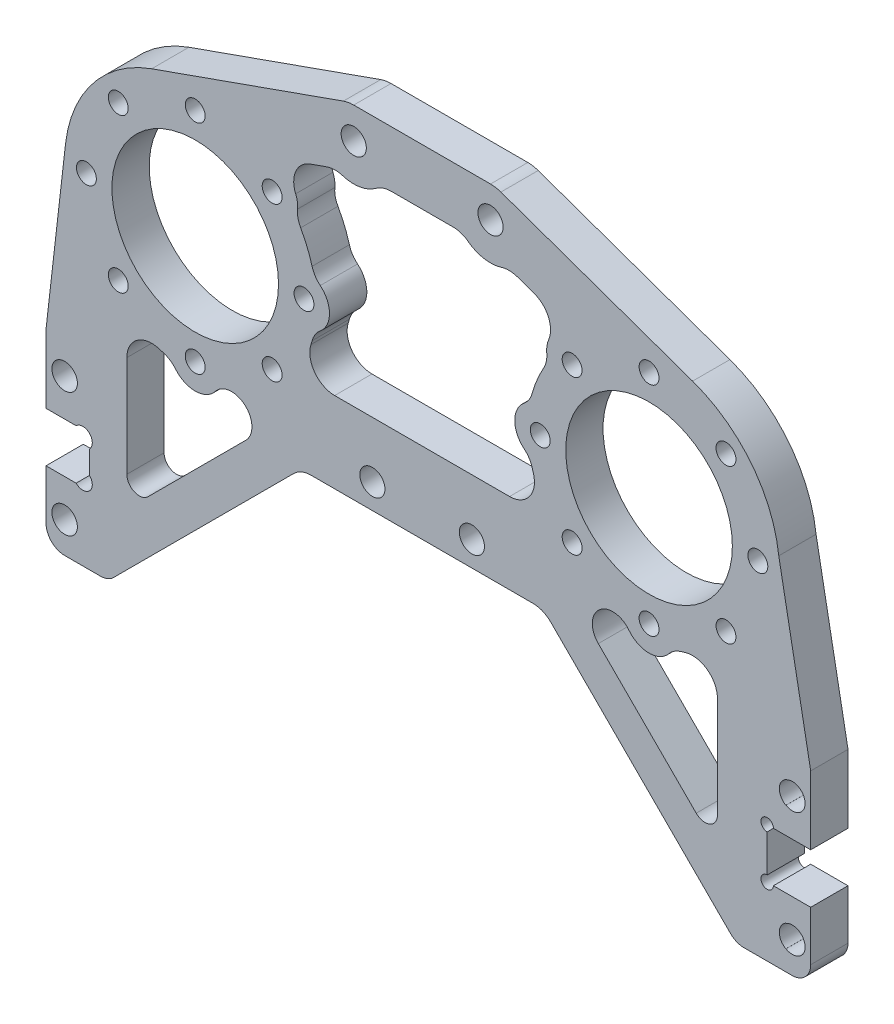
SolidWorks part; units mm, degrees
material "Thornel Mat VMA"
ref_plane "前视基准面" through (0, 0, 0) normal (0, 0, 1) x (1, 0, 0)
ref_plane "上视基准面" through (0, 0, 0) normal (0, 1, 0) x (1, 0, 0)
ref_plane "右视基准面" through (0, 0, 0) normal (1, 0, 0) x (0, 0, -1)
sketch "草图1" plane through (0, 0, 0) normal (0, 0, 1) x (1, 0, 0)
  line L0 (-36.5, 0) -> (36.5, 0) construction
  line L1 (-43.5079, -19.7962) -> (-12.6685, -30.7134)
  line L2 (11, -26) -> (-11, -26) construction
  line L3 (11, -26) -> (11, 26) construction
  line L4 (11, 26) -> (-11, 26) construction
  line L5 (-11, -26) -> (-11, 26) construction
  line L6 (11, -26) -> (-11, 26) construction
  line L7 (11, 26) -> (-11, -26) construction
  line L8 (-11, -31) -> (11, -31)
  line L9 (12.6685, -30.7134) -> (43.5079, -19.7962)
  line L10 (43.5079, 19.7962) -> (12.6685, 30.7134)
  line L11 (11, 31) -> (-11, 31)
  line L12 (-12.6685, 30.7134) -> (-43.5079, 19.7962)
  line L13 (0, 26) -> (0, -20) construction
  line L14 (0, -20) -> (-8, -20) construction
  circle A0 centre (-11, 26) radius 2.025
  circle A1 centre (11, 26) radius 2.025
  circle A2 centre (11, -26) radius 2.025 construction
  circle A3 centre (-11, -26) radius 2.025 construction
  circle A4 centre (-36.5, 0) radius 13.4
  circle A5 centre (-36.5, 0) radius 17.5 construction
  circle A6 centre (-19, 0) radius 1.6
  circle A7 centre (-24.1256, -12.3744) radius 1.6
  circle A8 centre (-36.5, -17.5) radius 1.6
  circle A9 centre (-48.8744, -12.3744) radius 1.6
  circle A10 centre (-54, 0) radius 1.6
  circle A11 centre (-48.8744, 12.3744) radius 1.6
  circle A12 centre (-36.5, 17.5) radius 1.6
  circle A13 centre (-24.1256, 12.3744) radius 1.6
  circle A14 centre (36.5, 0) radius 13.4
  circle A15 centre (36.5, 0) radius 17.5 construction
  circle A16 centre (19, 0) radius 1.6
  circle A17 centre (24.1256, 12.3744) radius 1.6
  circle A18 centre (36.5, 17.5) radius 1.6
  circle A19 centre (48.8744, 12.3744) radius 1.6
  circle A20 centre (54, 0) radius 1.6
  circle A21 centre (48.8744, -12.3744) radius 1.6
  circle A22 centre (36.5, -17.5) radius 1.6
  circle A23 centre (24.1256, -12.3744) radius 1.6
  arc A24 (43.5079, -19.7962) -> (43.5079, 19.7962) centre (36.5, 0) ccw
  arc A25 (-43.5079, -19.7962) -> (-43.5079, 19.7962) centre (-36.5, 0) cw
  arc A26 (12.6685, 30.7134) -> (11, 31) centre (11, 26) ccw
  arc A27 (-11, 31) -> (-12.6685, 30.7134) centre (-11, 26) ccw
  arc A28 (11, -31) -> (12.6685, -30.7134) centre (11, -26) ccw
  arc A29 (-12.6685, -30.7134) -> (-11, -31) centre (-11, -26) ccw
  circle A30 centre (-8, -20) radius 2.025
  circle A31 centre (8, -20) radius 2.025
  point P3 (0, 0)
  point P32 (-36.5, 0)
  point P51 (36.5, 0)
  dimension "D4" = 4.05
  dimension "D5" = 26.8
  dimension "D6" = 35
  dimension "D7" = 3.2
  dimension "D10" = 21
  dimension "D11" = 5
  dimension "D13" = 16
  dimension "D1" = 73
  dimension "D2" = 22
  dimension "D3" = 52
  dimension "D12" = 46
  dimension "D8" = 8
  dimension "D9" = 8
extrude "凸台-拉伸1" add sketch "草图1" along normal blind 6
chamfer "倒角1" distance 2.2 angle 45 2 edges at (-8.975, 26, 0) (13.025, 26, 0)
sketch "草圖2" plane through (0, 0, 0) normal (0, 0, -1) x (-1, 0, 0)
  line L9 (60.5, -55) -> (0, -55)
  line L10 (0, -55) -> (0, -31)
  line L11 (11, -31) -> (-11, -31) construction
  line L12 (0, -31) -> (43.5079, -19.7962)
  line L13 (43.5079, -19.7962) -> (12.6685, -30.7134) construction
  line L14 (57.5, -30) -> (57.5, -50) construction
  line L15 (60.5, -44) -> (53.5, -44)
  line L17 (60.5, -36) -> (53.5, -36)
  line L18 (53.5, -44) -> (53.5, -36)
  line L19 (60.5, -55) -> (60.5, -44)
  line L20 (60.5, -36) -> (60.5, -25)
  line L21 (0, 0) -> (0, 58.3141) construction
  line L22 (60.5, -25) -> (57.3637, 2.3891)
  arc A0 (39.9252, -20.7188) -> (57.5, 0) centre (36.5, 0) ccw construction
  arc A2 (43.5079, -19.7962) -> (43.5079, 19.7962) centre (36.5, 0) ccw construction
  circle A3 centre (36.5, 0) radius 21 construction
  arc A4 (43.5079, -19.7962) -> (57.3637, 2.3891) centre (36.5, 0) ccw
  circle A6 centre (57.5, -40) radius 4 construction
  circle A7 centre (57.5, -30) radius 2.05
  circle A8 centre (57.5, -50) radius 2.05
  dimension "D3" = 115
  dimension "D4" = 8
  dimension "D5" = 4.1
  dimension "D1" = 3
  dimension "D2" = 40
  dimension "D6" = 20
  dimension "D7" = 24
extrude "填料-伸長1" add sketch "草圖2" against normal up to surface (6 mm away)
sketch "草图3" plane through (0, 0, 0) normal (0, 0, -1) x (-1, 0, 0)
  line L4 (60.5, -55) -> (60.5, -44) construction
  line L6 (50.5, -55) -> (20.6716, -25.1716)
  line L11 (17.8431, -24) -> (0, -24)
  line L13 (0, -24) -> (0, -55)
  line L14 (0, -55) -> (50.5, -55)
  circle A0 centre (8, -20) radius 2.025 construction
  arc A1 (20.6716, -25.1716) -> (17.8431, -24) centre (17.8431, -28) ccw
  dimension "D4" = 4
  dimension "D3" = 4
  dimension "D1" = 45
  dimension "D2" = 10
extrude "切除-拉伸2" cut sketch "草图3" against normal through all
sketch "草图4" plane through (0, 0, 0) normal (0, 0, -1) x (-1, 0, 0)
  line L0 (55.6567, -36) -> (53.5, -38.1567) construction
  line L3 (53.5, -41.8433) -> (55.6567, -44) construction
  line L5 (60.5, -36) -> (53.5, -36) construction
  line L6 (53.5, -44) -> (53.5, -36) construction
  line L7 (60.5, -44) -> (53.5, -44) construction
  circle A0 centre (54.5783, -42.9217) radius 1.525
  circle A1 centre (54.5783, -37.0783) radius 1.525
  dimension "D1" = 3.05
  dimension "D2" = 45
  dimension "D3" = 45
extrude "切除-拉伸3" cut sketch "草图4" against normal through all
mirror "鏡射2" about plane through (0, 0, 0) normal (1, 0, 0) of "切除-拉伸3", "填料-伸長1", "切除-拉伸2"
fillet "圆角1" radius 3 4 edges at (60.5, -55, 3) (50.5, -55, 3) (-50.5, -55, 3) (-60.5, -55, 3)
sketch "草图5" plane through (0, 0, 0) normal (0, 0, -1) x (-1, 0, 0)
  line L0 (8, -20) -> (-8, -20) construction
  line L2 (-2, -25.5) -> (1, -25.5)
  line L3 (2, -24.5) -> (2, -6.5)
  line L4 (1, -5.5) -> (-2, -5.5)
  line L5 (-3, -24.5) -> (-3, -6.5)
  arc A0 (-2, -25.5) -> (-3, -24.5) centre (-2, -24.5) cw
  arc A1 (1, -5.5) -> (2, -6.5) centre (1, -6.5) cw
  arc A2 (1, -25.5) -> (2, -24.5) centre (1, -24.5) ccw
  arc A3 (-3, -6.5) -> (-2, -5.5) centre (-2, -6.5) cw
  point P11 (-0.5, -5.5)
  point P14 (-3, -25.5)
  point P17 (2, -5.5)
  point P20 (2, -25.5)
  point P23 (-3, -5.5)
  dimension "D4" = 1
  dimension "D1" = 5
  dimension "D2" = 5.5
  dimension "D3" = 20
  dimension "D5" = 2
extrude "切除-拉伸4" [suppressed] cut sketch "草图5" against normal through all
sketch "草图9" plane through (0, 0, 0) normal (0, 0, -1) x (-1, 0, 0)
  line L0 (47.5, -38.6863) -> (47.5, -22.4332)
  line L2 (28.3372, -24.3519) -> (44.0858, -40.1005)
  line L3 (0, 44.0083) -> (0, -69.3597) construction
  line L4 (-14.0668, -11) -> (14.0668, -11)
  line L5 (49.6213, -54.1213) -> (20.6716, -25.1716) construction
  line L9 (53.5, -41.8433) -> (53.5, -38.1567) construction
  line L10 (17.9923, 19.2815) -> (15.3212, 20.227)
  line L12 (-5, 22) -> (5, 22)
  line L14 (12.6685, 30.7134) -> (43.5079, 19.7962) construction
  line L15 (-11, 31) -> (11, 31) construction
  line L19 (17.8431, -24) -> (-17.8431, -24) construction
  line L20 (-17.9923, 19.2815) -> (-15.3212, 20.227)
  line L21 (-28.3372, -24.3519) -> (-44.0858, -40.1005)
  line L22 (-47.5, -38.6863) -> (-47.5, -22.4332)
  arc A1 (33.26, -20.0125) -> (28.3372, -24.3519) centre (30.662, -22.0272) ccw
  arc A2 (47.5, -38.6863) -> (44.0858, -40.1005) centre (45.5, -38.6863) cw
  arc A3 (7.4, 21.2) -> (12.7918, 20.2738) centre (11, 26) ccw
  arc A4 (19.5414, 9.6258) -> (17.702, 5.1851) centre (36.5, 0) ccw
  arc A6 (5, 22) -> (7.4, 21.2) centre (5, 18) cw
  arc A7 (15.3212, 20.227) -> (12.7918, 20.2738) centre (13.9864, 16.4563) ccw
  arc A8 (17.9923, 19.2815) -> (20.3455, 13.9619) centre (16.6575, 15.5108) cw
  arc A9 (14.0668, -11) -> (17.8852, -5.8085) centre (14.0668, -7) ccw
  arc A10 (42.3085, -18.6148) -> (47.5, -22.4332) centre (43.5, -22.4332) cw
  arc A21 (33.26, -20.0125) -> (39.6629, -20.1088) centre (36.5, -17.5) ccw
  arc A22 (16.3912, 3.1629) -> (16.3912, -3.1629) centre (19, 0) ccw
  arc A23 (20.3455, 13.9619) -> (20.0444, 11.9826) centre (24.1256, 12.3744) ccw
  arc A24 (41.6851, -18.798) -> (42.3085, -18.6148) centre (36.5, 0) ccw
  arc A25 (17.702, -5.1851) -> (17.8852, -5.8085) centre (36.5, 0) ccw
  circle A26 centre (36.5, -17.5) radius 1.6 construction
  arc A27 (16.3912, 3.1629) -> (17.702, 5.1851) centre (13.846, 6.2487) ccw
  arc A28 (16.3912, -3.1629) -> (17.702, -5.1851) centre (13.846, -6.2487) cw
  arc A29 (39.6629, -20.1088) -> (41.6851, -18.798) centre (42.7487, -22.654) cw
  arc A30 (20.0444, 11.9826) -> (19.5414, 9.6258) centre (16.0627, 11.6003) cw
  arc A31 (-20.0444, 11.9826) -> (-19.5414, 9.6258) centre (-16.0627, 11.6003) ccw
  arc A32 (-39.6629, -20.1088) -> (-41.6851, -18.798) centre (-42.7487, -22.654) ccw
  arc A33 (-16.3912, -3.1629) -> (-17.702, -5.1851) centre (-13.846, -6.2487) ccw
  arc A34 (-16.3912, 3.1629) -> (-17.702, 5.1851) centre (-13.846, 6.2487) cw
  arc A35 (-17.702, -5.1851) -> (-17.8852, -5.8085) centre (-36.5, 0) cw
  arc A36 (-41.6851, -18.798) -> (-42.3085, -18.6148) centre (-36.5, 0) cw
  arc A37 (-20.3455, 13.9619) -> (-20.0444, 11.9826) centre (-24.1256, 12.3744) cw
  arc A38 (-16.3912, 3.1629) -> (-16.3912, -3.1629) centre (-19, 0) cw
  arc A39 (-33.26, -20.0125) -> (-39.6629, -20.1088) centre (-36.5, -17.5) cw
  arc A40 (-42.3085, -18.6148) -> (-47.5, -22.4332) centre (-43.5, -22.4332) ccw
  arc A41 (-14.0668, -11) -> (-17.8852, -5.8085) centre (-14.0668, -7) cw
  arc A42 (-17.9923, 19.2815) -> (-20.3455, 13.9619) centre (-16.6575, 15.5108) ccw
  arc A43 (-15.3212, 20.227) -> (-12.7918, 20.2738) centre (-13.9864, 16.4563) cw
  arc A44 (-5, 22) -> (-7.4, 21.2) centre (-5, 18) ccw
  arc A45 (-19.5414, 9.6258) -> (-17.702, 5.1851) centre (-36.5, 0) cw
  arc A46 (-7.4, 21.2) -> (-12.7918, 20.2738) centre (-11, 26) cw
  arc A47 (-47.5, -38.6863) -> (-44.0858, -40.1005) centre (-45.5, -38.6863) ccw
  arc A48 (-33.26, -20.0125) -> (-28.3372, -24.3519) centre (-30.662, -22.0272) cw
  point P43 (0, -11)
  point P57 (17.366, -3.7603)
  point P103 (0, 22)
  dimension "D3" = 39
  dimension "D4" = 2
  dimension "D5" = 4
  dimension "D7" = 12
  dimension "D10" = 4
  dimension "D11" = 4
  dimension "D12" = 2.5
  dimension "D1" = 6
  dimension "D2" = 6
  dimension "D6" = 9
  dimension "D8" = 9
  dimension "D9" = 13
extrude "切除-拉伸6" cut sketch "草图9" against normal through all
sketch "草图10" plane through (0, 0, 0) normal (0, 0, -1) x (-1, 0, 0)
  line L0 (-53.5, -41.8433) -> (-53.5, -38.1567) construction
  line L1 (-60.5, -44) -> (-55.6567, -44) construction
  line L2 (-60.5, -36) -> (-55.6567, -36) construction
  line L3 (-60.5, -36) -> (-60.5, -25) construction
  line L4 (-60.5, -52) -> (-60.5, -44) construction
  line L5 (-53.5, -41.8433) -> (-53.5, -38.1567) construction
  line L6 (-60.5, -44) -> (-55.6567, -44) construction
  line L7 (-60.5, -36) -> (-55.5, -36) construction
  line L8 (-60.5, -36) -> (-60.5, -25) construction
  line L9 (-60.5, -52) -> (-60.5, -44) construction
  line L11 (-62.5, -44) -> (-57.6567, -44)
  line L12 (-62.5, -36) -> (-57.5, -36)
  line L13 (-62.5, -36) -> (-62.5, -25)
  line L14 (-62.5, -52) -> (-62.5, -44)
  line L15 (-62.5, -25) -> (-57.3637, 2.3891)
  line L16 (-55.5, -41.8433) -> (-55.5, -38.1567) [skipped]
  line L17 (-59.5, -55) -> (-51.7426, -55)
  line L18 (-57.5, -55) -> (-51.7426, -55) construction
  line L19 (-51.7426, -55) -> (-51.7426, -25)
  line L20 (-51.7426, -25) -> (-57.3637, 2.3891)
  line L21 (-60.5, -25) -> (-57.3637, 2.3891) construction
  line L22 (-57.5, -36) -> (-55.5, -36)
  line L24 (-55.5, -36) -> (-55.5, -44)
  line L25 (-55.5, -44) -> (-57.6567, -44)
  arc A0 (-60.5, -52) -> (-57.5, -55) centre (-57.5, -52) ccw construction
  circle A1 centre (-57.5, -30) radius 2.05 construction
  circle A2 centre (-57.5, -50) radius 2.05 construction
  arc A3 (-60.5, -52) -> (-57.5, -55) centre (-57.5, -52) ccw construction
  circle A4 centre (-57.5, -30) radius 2.05 construction
  circle A5 centre (-57.5, -50) radius 2.05 construction
  arc A6 (-62.5, -52) -> (-59.5, -55) centre (-59.5, -52) ccw
  circle A7 centre (-59.5, -30) radius 2.05
  circle A8 centre (-59.5, -50) radius 2.05
  arc A9 (-43.5079, 19.7962) -> (-57.3637, 2.3891) centre (-36.5, 0) ccw construction
  arc A10 (-51.7426, -55) -> (-49.6213, -54.1213) centre (-51.7426, -52) ccw construction
  dimension "D2" = 2
  dimension "D3" = 2
  dimension "D1" = 2
extrude "凸台-拉伸2" add sketch "草图10" against normal blind 6
sketch "草图11" plane through (0, 0, 0) normal (0, 0, 1) x (1, 0, 0)
  circle A0 centre (59.55, -30) radius 2.05
  arc A1 (58.5, -31.7896) -> (58.5, -28.2104) centre (57.5, -30) ccw construction
  circle A2 centre (59.55, -50) radius 2.05
  arc A3 (58.5, -51.7896) -> (58.5, -48.2104) centre (57.5, -50) ccw construction
  circle A4 centre (55.5, -36) radius 1
  circle A5 centre (55.5, -44) radius 1
  dimension "D1" = 2
  dimension "D2" = 4.1
extrude "切除-拉伸8" cut sketch "草图11" along normal through all
